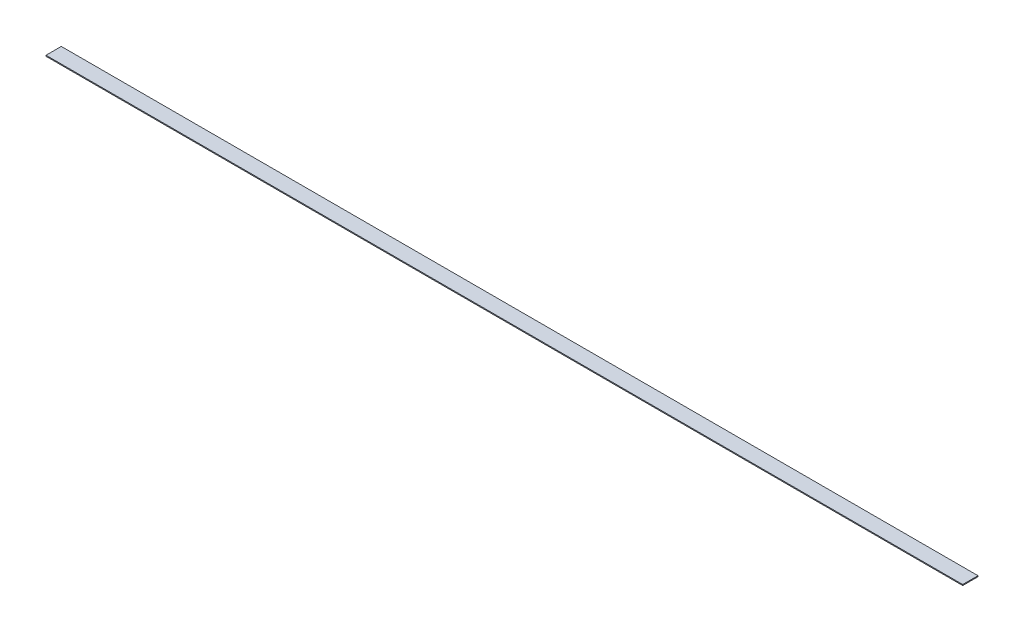
SolidWorks part; units mm, degrees
ref_plane "Front Plane" through (0, 0, 0) normal (0, 0, 1) x (1, 0, 0)
ref_plane "Top Plane" through (0, 0, 0) normal (0, 1, 0) x (1, 0, 0)
ref_plane "Right Plane" through (0, 0, 0) normal (1, 0, 0) x (0, 0, -1)
sketch "Sketch1" plane through (0, 0, 0) normal (0, 1, 0) x (1, 0, 0)
  line L1 (0, 0) -> (1524, 0)
  line L2 (0, 0) -> (0, 25.4)
  line L3 (0, 25.4) -> (1524, 25.4)
  line L4 (1524, 0) -> (1524, 25.4)
  dimension "D1" = 25.4
  dimension "D2" = 1524
extrude "Boss-Extrude1" add sketch "Sketch1" along normal blind 1.5875
